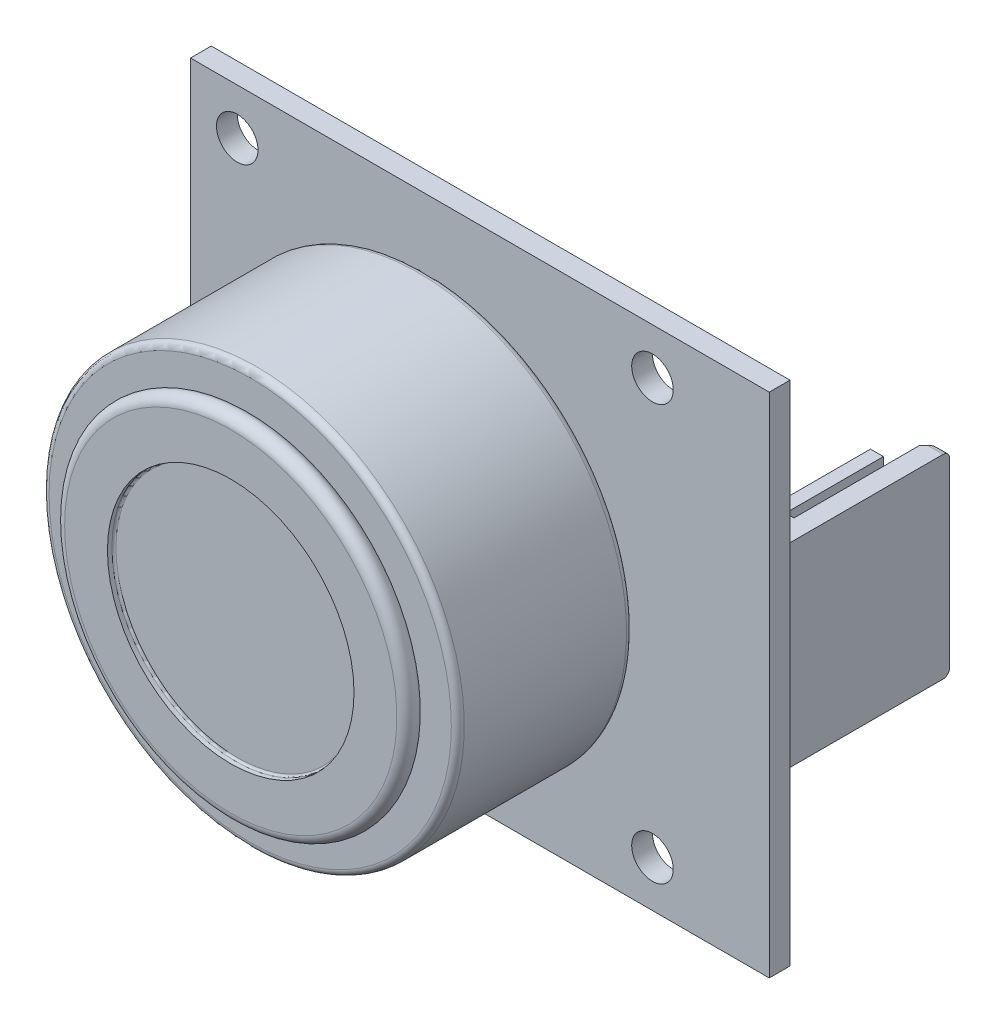
SolidWorks part; units mm, degrees
ref_plane "Front Plane" through (0, 0, 0) normal (0, 0, 1) x (1, 0, 0)
ref_plane "Top Plane" through (0, 0, 0) normal (0, 1, 0) x (1, 0, 0)
ref_plane "Right Plane" through (0, 0, 0) normal (1, 0, 0) x (0, 0, -1)
sketch "Sketch1" plane through (0, 0, 0) normal (0, 0, 1) x (1, 0, 0)
  line L0 (-22.3, -19.55) -> (22.3, 19.55) construction
  line L1 (-22.3, -19.55) -> (22.3, -19.55)
  line L2 (-22.3, -19.55) -> (-22.3, 19.55)
  line L3 (-22.3, 19.55) -> (22.3, 19.55)
  line L4 (22.3, -19.55) -> (22.3, 19.55)
  line L5 (0, 0) -> (-11.5209, 0) construction
  circle A1 centre (13.3, 16) radius 1.6
  circle A2 centre (13.3, -16) radius 1.6
  circle A3 centre (-18.7, -16) radius 1.6
  circle A4 centre (-18.7, 16) radius 1.6
  point P4 (0, 0)
  point P16 (0, 0)
  dimension "D3" = 3.2
  dimension "D1" = 39.1
  dimension "D2" = 44.6
  dimension "D4" = 3.6
  dimension "D6" = 32
  dimension "D7" = 32
extrude "Boss-Extrude1" add sketch "Sketch1" along normal blind 1.6
sketch "Sketch3" plane through (0, 0, 0) normal (0, 1, 0) x (1, 0, 0)
  line L0 (-2.7, 11.6143) -> (-2.7, -27.7056) construction
  line L1 (22.3, -1.6) -> (22.3, 0) construction
  line L2 (-2.7, -1.6) -> (-15.7, -1.6)
  line L3 (22.3, -1.6) -> (-22.3, -1.6) construction
  line L4 (-15.7, -1.6) -> (-15.7, -2.9436)
  line L5 (-15.8564, -3.1) -> (-18.2, -3.1)
  line L6 (-18.7, -3.6) -> (-18.7, -16.1)
  line L7 (-18.2, -16.6) -> (-15.5, -16.6)
  line L9 (-15.5, -18.1) -> (-12.2, -18.1)
  line L10 (-2.7, -17.6) -> (-2.7, -1.6)
  line L11 (-12.2, -18.1) -> (-12.2, -17.7564)
  line L12 (-12.0436, -17.6) -> (-2.7, -17.6)
  arc A0 (-15.5, -16.6) -> (-15.5, -18.1) centre (-15.5, -17.35) ccw
  arc A1 (-18.2, -16.6) -> (-18.7, -16.1) centre (-18.2, -16.1) cw
  arc A2 (-18.7, -3.6) -> (-18.2, -3.1) centre (-18.2, -3.6) cw
  arc A3 (-12.2, -17.7564) -> (-12.0436, -17.6) centre (-12.0436, -17.7564) cw
  arc A4 (-15.7, -2.9436) -> (-15.8564, -3.1) centre (-15.8564, -2.9436) cw
  point P15 (-16.25, -17.35)
  point P20 (-18.7, -16.6)
  point P23 (-18.7, -3.1)
  dimension "D10" = 0.5
  dimension "D11" = 0.1564
  dimension "D1" = 25
  dimension "D2" = 32
  dimension "D3" = 26
  dimension "D4" = 16.5
  dimension "D5" = 13.5
  dimension "D6" = 27.1
  dimension "D7" = 1.5
  dimension "D8" = 19
  dimension "D9" = 0.5
revolve "Revolve1" add sketch "Sketch3" angle 360 about L0
sketch "Sketch5" plane through (0, 0, 0) normal (0, 0, -1) x (-1, 0, 0)
  line L0 (-21.1, 0) -> (0, 0) construction
  line L1 (-21.1, 7.5) -> (-15.1, 7.5)
  line L2 (-21.1, 7.5) -> (-21.1, -7.5)
  line L3 (-21.1, -7.5) -> (-15.1, -7.5)
  line L4 (-15.1, 7.5) -> (-15.1, -7.5)
  line L6 (-22.3, -19.55) -> (-22.3, 19.55) construction
  dimension "D1" = 15
  dimension "D2" = 1.2
  dimension "D3" = 6
extrude "Boss-Extrude2" add sketch "Sketch5" along normal blind 13.5
sketch "Sketch6" plane through (0, 0, -13.5) normal (0, 0, -1) x (-1, 0, 0)
  line L0 (-15.1, 7.5) -> (-21.1, 7.5) construction
  line L1 (-19.6, 7.5) -> (-15.1, 7.5)
  line L2 (-19.6, 7.5) -> (-19.6, -7.5)
  line L3 (-19.6, -7.5) -> (-15.1, -7.5)
  line L4 (-15.1, 7.5) -> (-15.1, -7.5)
  line L5 (-17.8, 7.5) -> (-17.8, -7.5) construction
  line L6 (-17.3, 6.85) -> (-18.3, 6.85)
  line L7 (-17.3, 6.85) -> (-17.3, 5.85)
  line L8 (-17.3, 5.85) -> (-18.3, 5.85)
  line L9 (-18.3, 6.85) -> (-18.3, 5.85)
  line L10 (-17.3, 4.31) -> (-18.3, 4.31)
  line L11 (-17.3, 4.31) -> (-17.3, 3.31)
  line L12 (-17.3, 3.31) -> (-18.3, 3.31)
  line L13 (-18.3, 4.31) -> (-18.3, 3.31)
  line L14 (-17.3, 1.77) -> (-18.3, 1.77)
  line L15 (-17.3, 1.77) -> (-17.3, 0.77)
  line L16 (-17.3, 0.77) -> (-18.3, 0.77)
  line L17 (-18.3, 1.77) -> (-18.3, 0.77)
  line L18 (-17.3, -0.77) -> (-18.3, -0.77)
  line L19 (-17.3, -0.77) -> (-17.3, -1.77)
  line L20 (-17.3, -1.77) -> (-18.3, -1.77)
  line L21 (-18.3, -0.77) -> (-18.3, -1.77)
  line L22 (-17.3, -3.31) -> (-18.3, -3.31)
  line L23 (-17.3, -3.31) -> (-17.3, -4.31)
  line L24 (-17.3, -4.31) -> (-18.3, -4.31)
  line L25 (-18.3, -3.31) -> (-18.3, -4.31)
  line L26 (-18.3, 6.35) -> (-17.3, 6.35) construction
  line L27 (-18.3, 3.81) -> (-17.3, 3.81) construction
  line L28 (-18.3, 1.27) -> (-17.3, 1.27) construction
  line L29 (-18.3, -1.27) -> (-17.3, -1.27) construction
  line L30 (-18.3, -3.81) -> (-17.3, -3.81) construction
  line L31 (-17.3, -5.85) -> (-18.3, -5.85)
  line L32 (-17.3, -5.85) -> (-17.3, -6.85)
  line L33 (-17.3, -6.85) -> (-18.3, -6.85)
  line L34 (-18.3, -5.85) -> (-18.3, -6.85)
  line L35 (-18.3, -6.35) -> (-17.3, -6.35) construction
  dimension "D1" = 4.5
  dimension "D2" = 1
  dimension "D3" = 1.8
  dimension "D4" = 2.54
  dimension "D5" = 2.54
  dimension "D6" = 2.54
  dimension "D7" = 2.54
  dimension "D8" = 2.54
  dimension "D9" = 0.65
  dimension "D10" = 0.65
extrude "Cut-Extrude2" cut sketch "Sketch6" against normal blind 10.5
sketch "Sketch7" plane through (0, 0, -13.5) normal (0, 0, -1) x (-1, 0, 0)
  line L1 (-18.3, 6.85) -> (-17.3, 6.85)
  line L2 (-18.3, 6.85) -> (-18.3, -6.85)
  line L3 (-18.3, -6.85) -> (-17.3, -6.85)
  line L4 (-17.3, 6.85) -> (-17.3, -6.85)
extrude "Cut-Extrude3" cut sketch "Sketch7" against normal blind 2
chamfer "Chamfer1" distance 0.3 angle 45 24 edges at (17.8, -5.85, -11.5) (17.3, -6.35, -11.5) (17.8, -6.85, -11.5) (18.3, -6.35, -11.5) (17.8, -4.31, -11.5) (18.3, -3.81, -11.5) (17.8, -3.31, -11.5) (17.3, -3.81, -11.5) (17.8, -1.77, -11.5) (18.3, -1.27, -11.5) (17.8, -0.77, -11.5) (17.3, -1.27, -11.5) (17.8, 0.77, -11.5) (18.3, 1.27, -11.5) (17.8, 1.77, -11.5) (17.3, 1.27, -11.5) (17.8, 3.31, -11.5) (18.3, 3.81, -11.5) (17.8, 4.31, -11.5) (17.3, 3.81, -11.5) (17.8, 5.85, -11.5) (18.3, 6.35, -11.5) (17.8, 6.85, -11.5) (17.3, 6.35, -11.5)
chamfer "Chamfer2" distance 0.8 angle 45 1 edges at (19.6, 0, -13.5)
fillet "Fillet1" radius 0.5 2 edges at (20.75, -7.5, -13.5) (20.75, 7.5, -13.5)
